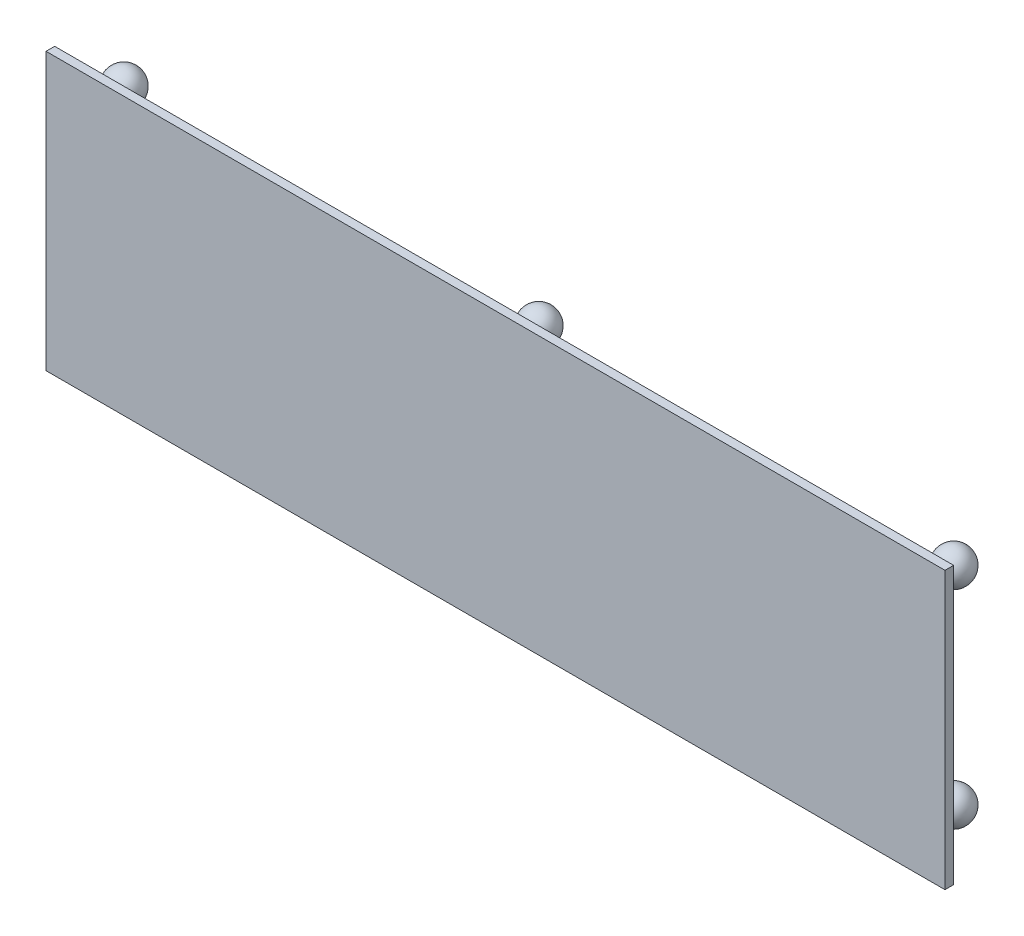
SolidWorks part; units mm, degrees
ref_plane "Front Plane" through (0, 0, 0) normal (0, 0, 1) x (1, 0, 0)
ref_plane "Top Plane" through (0, 0, 0) normal (0, 1, 0) x (1, 0, 0)
ref_plane "Right Plane" through (0, 0, 0) normal (1, 0, 0) x (0, 0, -1)
sketch "Sketch1" plane through (0, 0, 0) normal (0, 0, 1) x (1, 0, 0)
  line L1 (-330.2, -101.6) -> (330.2, -101.6)
  line L2 (-330.2, -101.6) -> (-330.2, 101.6)
  line L3 (-330.2, 101.6) -> (330.2, 101.6)
  line L4 (330.2, -101.6) -> (330.2, 101.6)
  line L5 (-330.2, -101.6) -> (330.2, 101.6) construction
  line L6 (-330.2, 101.6) -> (330.2, -101.6) construction
  point P0 (0, 0)
  dimension "D1" = 203.2
  dimension "D2" = 660.4
extrude "Boss-Extrude1" add sketch "Sketch1" along normal blind 6.35
sketch "Sketch3" plane through (0, 0, 0) normal (1, 0, 0) x (0, 0, -1)
  line L0 (0, 76.2) -> (0, -76.2) construction
  line L1 (0, -101.6) -> (0, 101.6) construction
  line L2 (0, -76.2) -> (38.1, -76.2)
  line L3 (0, -82.1093) -> (14.1586, -82.1093)
  line L4 (0, -76.2) -> (0, -82.1093)
  line L5 (0, -76.2) -> (0, 0) construction
  line L6 (0, -76.2) -> (0, 0) construction
  line L8 (0, -36.3257) -> (73.4145, -36.3257) construction
  line L9 (0, 0) -> (101.3019, 0) construction
  arc A0 (14.1586, -82.1093) -> (38.1, -76.2) centre (25.4, -76.2) ccw
  point P6 (0, 0)
  dimension "D2" = 25.4
  dimension "D1" = 152.4
  dimension "D3" = 25.4
revolve "Revolve1" add sketch "Sketch3" angle 360 about L2
mirror "Mirror1" about plane through (0, 0, 0) normal (0, 1, 0) of "Revolve1"
pattern_linear "LPattern1" count 2 spacing 304.8 along (1, 0, 0) count 2 spacing 304.8 along (-1, 0, 0) of "Revolve1", "Mirror1"
